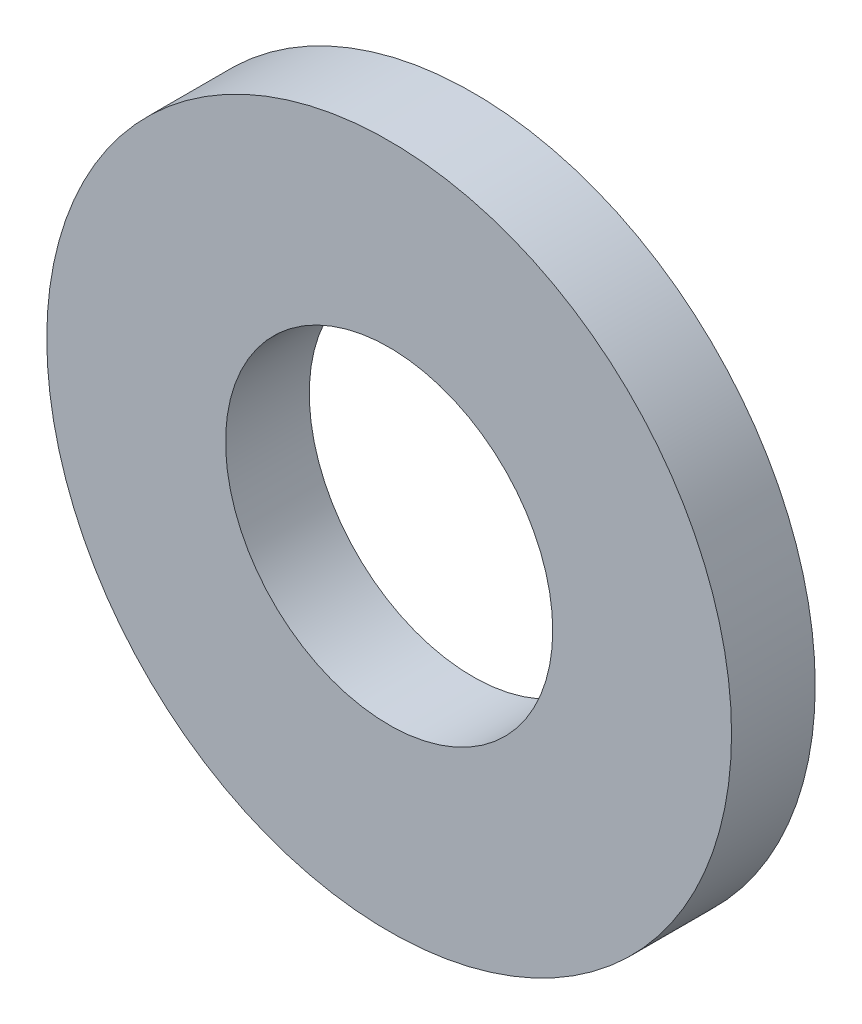
SolidWorks part; units mm, degrees
material "Nylon 101"
ref_plane "Front Plane" through (0, 0, 0) normal (0, 0, 1) x (1, 0, 0)
ref_plane "Top Plane" through (0, 0, 0) normal (0, 1, 0) x (1, 0, 0)
ref_plane "Right Plane" through (0, 0, 0) normal (1, 0, 0) x (0, 0, -1)
sketch "Sketch1" plane through (0, 0, 0) normal (0, 0, 1) x (1, 0, 0)
  circle A0 centre (0, 0) radius 4.5
  circle A1 centre (0, 0) radius 2.15
  dimension "OD" = 9
  dimension "ID1" = 4.3
extrude "Boss-Extrude1" add sketch "Sketch1" along normal blind 1.1
